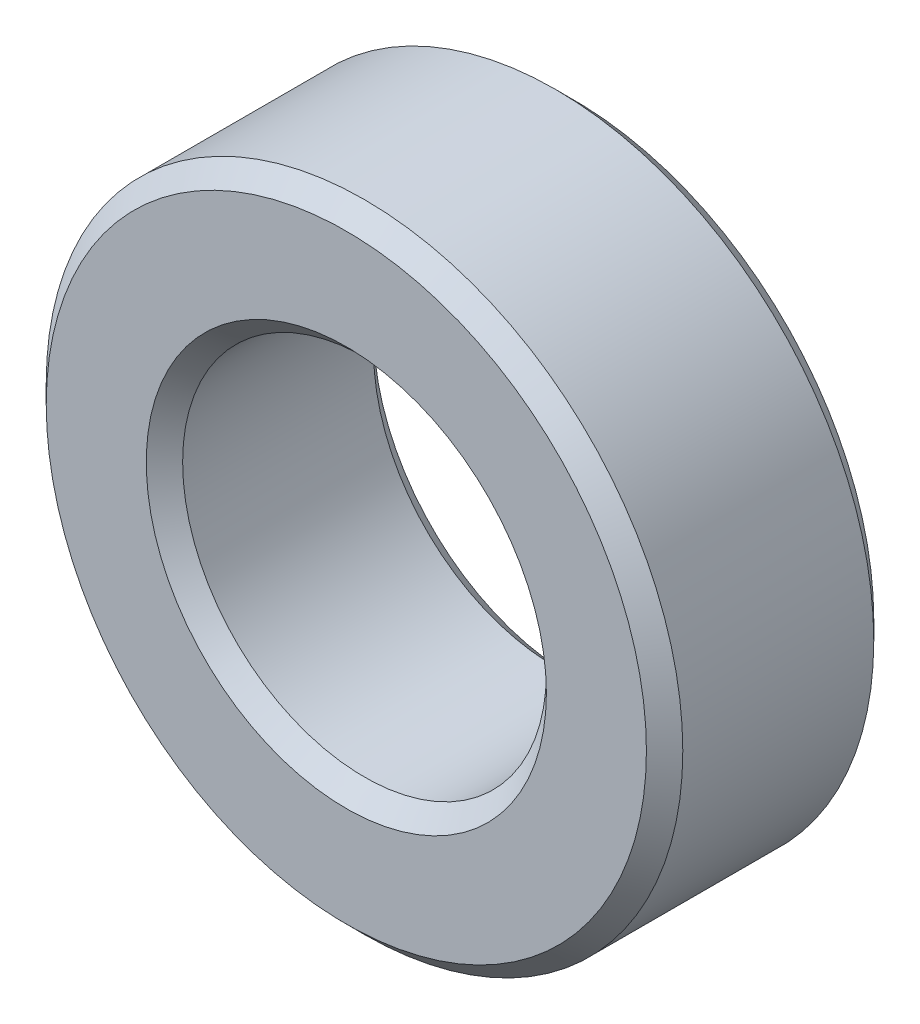
SolidWorks part; units mm, degrees
material "AISI 304"
ref_plane "Front Plane" through (0, 0, 0) normal (0, 0, 1) x (1, 0, 0)
ref_plane "Top Plane" through (0, 0, 0) normal (0, 1, 0) x (1, 0, 0)
ref_plane "Right Plane" through (0, 0, 0) normal (1, 0, 0) x (0, 0, -1)
sketch "Sketch1" plane through (0, 0, 0) normal (0, 0, 1) x (1, 0, 0)
  circle A0 centre (0, 0) radius 3.5
  circle A1 centre (0, 0) radius 2
  dimension "D1" = 7
  dimension "D2" = 4
extrude "Boss-Extrude1" add sketch "Sketch1" along normal blind 2.5
chamfer "Chamfer1" distance 0.2 angle 45 4 edges at (2, 0, 0) (3.5, 0, 0) (2, 0, 2.5) (3.5, 0, 2.5)
